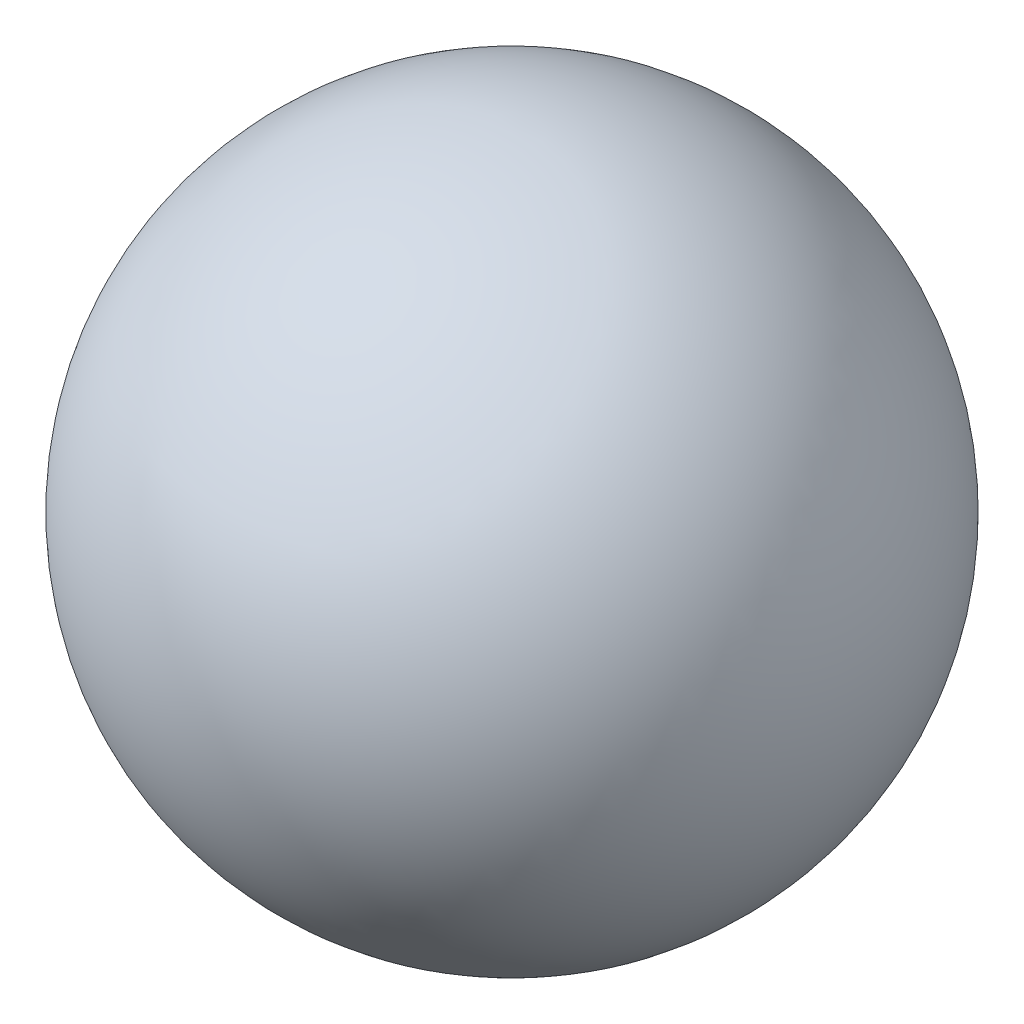
SolidWorks part; units mm, degrees
ref_plane "Alzado" through (0, 0, 0) normal (0, 0, 1) x (1, 0, 0)
ref_plane "Planta" through (0, 0, 0) normal (0, 1, 0) x (1, 0, 0)
ref_plane "Vista lateral" through (0, 0, 0) normal (1, 0, 0) x (0, 0, -1)
sketch "Croquis1" plane through (0, 0, 0) normal (0, 0, 1) x (1, 0, 0)
  line L0 (0, 10.6376) -> (0, 15.8756) construction
  line L1 (0, 4.65) -> (0, -4.65)
  arc A0 (0, 4.65) -> (0, -4.65) centre (0, 0) ccw
  dimension "D1" = 4.65
revolve "Revolución10" add sketch "Croquis1" angle 360 about L0
